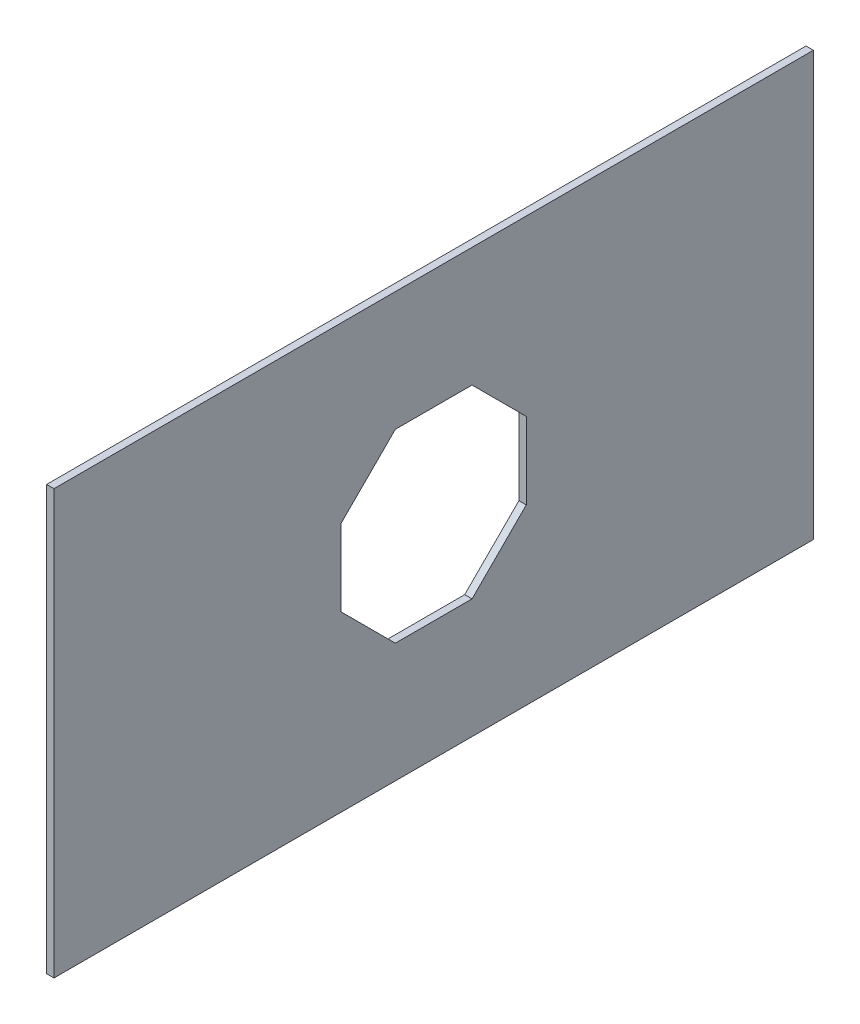
SolidWorks part; units mm, degrees
ref_plane "Front Plane" through (0, 0, 0) normal (0, 0, 1) x (1, 0, 0)
ref_plane "Top Plane" through (0, 0, 0) normal (0, 1, 0) x (1, 0, 0)
ref_plane "Right Plane" through (0, 0, 0) normal (1, 0, 0) x (0, 0, -1)
sketch "Sketch1" plane through (0, 0, 0) normal (1, 0, 0) x (0, 0, -1)
  line L1 (-246.0625, -137.3187) -> (246.0625, -137.3187)
  line L2 (-246.0625, -137.3187) -> (-246.0625, 137.3188)
  line L3 (-246.0625, 137.3188) -> (246.0625, 137.3188)
  line L4 (246.0625, -137.3187) -> (246.0625, 137.3188)
  line L5 (-246.0625, -137.3187) -> (246.0625, 137.3188) construction
  line L6 (-246.0625, 137.3188) -> (246.0625, -137.3187) construction
  point P0 (0, 0)
  dimension "D1" = 274.6375
  dimension "D2" = 492.125
extrude "Boss-Extrude1" add sketch "Sketch1" along normal blind 4.7625
sketch "Sketch2" plane through (4.7625, 0, 0) normal (1, 0, 0) x (0, 0, -1)
  line L0 (0, 0) -> (42.4264, 42.4264) construction
  line L1 (-24.8528, -60) -> (24.8528, -60)
  line L2 (-60, -24.8528) -> (-60, 24.8528)
  line L3 (-24.8528, 60) -> (24.8528, 60)
  line L4 (60, -24.8528) -> (60, 24.8528)
  line L5 (-42.4264, -42.4264) -> (42.4264, 42.4264) construction
  line L6 (0, 0) -> (-42.4264, 42.4264) construction
  line L7 (-42.4264, 42.4264) -> (-24.8528, 60) construction
  line L8 (0, 0) -> (42.4264, -42.4264) construction
  line L9 (-42.4264, 42.4264) -> (-60, 24.8528) construction
  line L10 (42.4264, -42.4264) -> (24.8528, -60) construction
  line L11 (42.4264, -42.4264) -> (60, -24.8528) construction
  line L12 (0, 0) -> (0, 60) construction
  line L13 (0, 0) -> (0, -60) construction
  line L14 (42.4264, 42.4264) -> (60, 24.8528) construction
  line L15 (42.4264, 42.4264) -> (24.8528, 60) construction
  line L16 (-42.4264, -42.4264) -> (-24.8528, -60) construction
  line L17 (-42.4264, -42.4264) -> (-60, -24.8528) construction
  line L18 (-24.8528, 60) -> (-60, 24.8528)
  line L19 (24.8528, 60) -> (60, 24.8528)
  line L20 (42.4264, -42.4264) -> (60, -24.8528)
  line L21 (24.8528, -60) -> (42.4264, -42.4264)
  line L22 (-60, -24.8528) -> (-24.8528, -60)
  point P0 (0, 0)
  dimension "D2" = 60
extrude "Cut-Extrude1" cut sketch "Sketch2" against normal up to next
